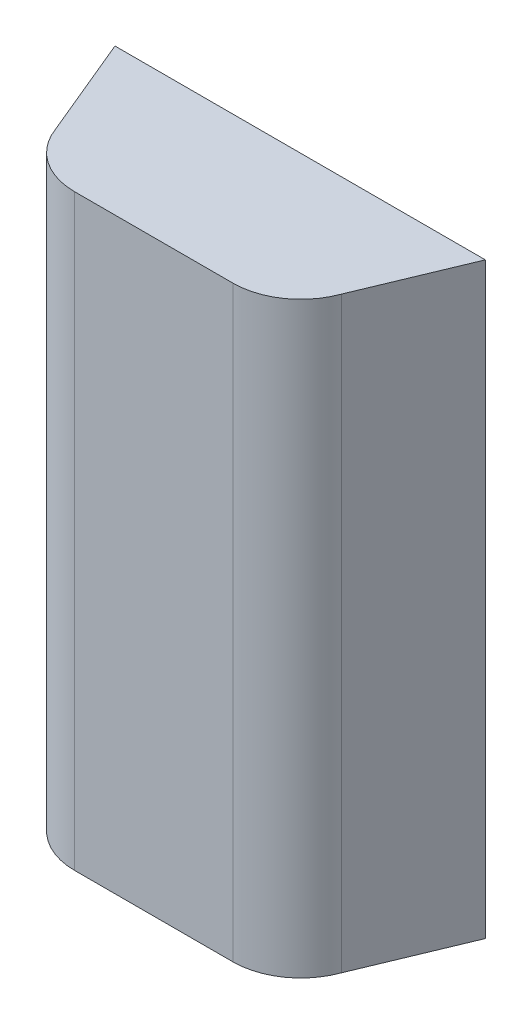
SolidWorks part; units mm, degrees
ref_plane "Front Plane" through (0, 0, 0) normal (0, 0, 1) x (1, 0, 0)
ref_plane "Top Plane" through (0, 0, 0) normal (0, 1, 0) x (1, 0, 0)
ref_plane "Right Plane" through (0, 0, 0) normal (1, 0, 0) x (0, 0, -1)
sketch "Sketch1" plane through (0, 0, 0) normal (0, 1, 0) x (1, 0, 0)
  line L1 (35, 0) -> (-35, 0)
  line L3 (-81.9087, 64.7394) -> (-63.1908, 19.7394)
  line L4 (-81.9087, 64.7394) -> (81.9087, 64.7394)
  line L5 (81.9087, 64.7394) -> (63.1908, 19.7394)
  arc A0 (-63.1908, 19.7394) -> (-35, 0) centre (-35, 30) ccw
  arc A1 (63.1908, 19.7394) -> (35, 0) centre (35, 30) cw
  point P10 (0, 0)
  point P13 (0, 64.7394)
  dimension "D2" = 45
  dimension "D1" = 35
extrude "Boss-Extrude1" add sketch "Sketch1" along normal blind 260
sketch "Sketch4" plane through (0, 0, 0) normal (0, -1, 0) x (1, 0, 0)
  line L1 (81.9087, -64.7394) -> (-81.9087, -64.7394) construction
  line L5 (-78.9087, -64.7394) -> (78.9087, -64.7394)
  line L6 (-35, -3) -> (35, -3)
  line L8 (-60.7889, -21.7644) -> (-78.9087, -64.7394)
  line L9 (60.7889, -21.7644) -> (78.9087, -64.7394)
  spline S0 degree 2 poles (-35, -3) (-54.7695, -6.8423) (-60.7889, -21.7644) knots 0 0 0 1 1 1
  spline S1 degree 2 poles (35, -3) (54.7695, -6.8423) (60.7889, -21.7644) knots 0 0 0 1 1 1
  point P6 (0, -64.7394)
  point P11 (0, -3)
extrude "Cut-Extrude1" cut sketch "Sketch4" against normal blind 256
